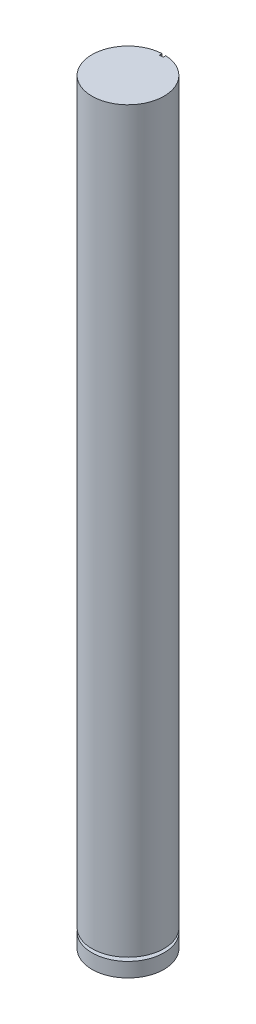
SolidWorks part; units mm, degrees
ref_plane "Front Plane" through (0, 0, 0) normal (0, 0, 1) x (1, 0, 0)
ref_plane "Top Plane" through (0, 0, 0) normal (0, 1, 0) x (1, 0, 0)
ref_plane "Right Plane" through (0, 0, 0) normal (1, 0, 0) x (0, 0, -1)
sketch "Sketch2" plane through (0, 0, 0) normal (0, 1, 0) x (1, 0, 0)
  circle A0 centre (0, 0) radius 20
  dimension "D1" = 40
extrude "Boss-Extrude1" add sketch "Sketch2" along normal blind 420
sketch "Sketch3" plane through (0, 0, 0) normal (1, 0, 0) x (0, 0, -1)
  line L0 (20, 10) -> (15, 10)
  line L1 (20, 0) -> (20, 420) construction
  line L2 (15, 10) -> (15, 8)
  line L3 (15, 8) -> (20, 8)
  line L4 (20, 8) -> (20, 10)
  line L5 (0, 0) -> (0, 32.6472) construction
  dimension "D1" = 5
  dimension "D2" = 2
  dimension "D3" = 8
revolve "Cut-Revolve1" cut sketch "Sketch3" angle 360 about L5
sketch "Sketch4" plane through (0, 420, 0) normal (0, 1, 0) x (1, 0, 0)
  line L0 (0, 0) -> (0, 20) construction
  line L2 (1, 20) -> (-1, 20)
  line L3 (1, 20) -> (1, 18.5)
  line L4 (1, 18.5) -> (-1, 18.5)
  line L5 (-1, 20) -> (-1, 18.5)
  circle A0 centre (0, 0) radius 20 construction
  dimension "D1" = 2
  dimension "D2" = 1.5
extrude "Cut-Extrude2" cut sketch "Sketch4" against normal blind 30 contours L4 L5 L2 L3
